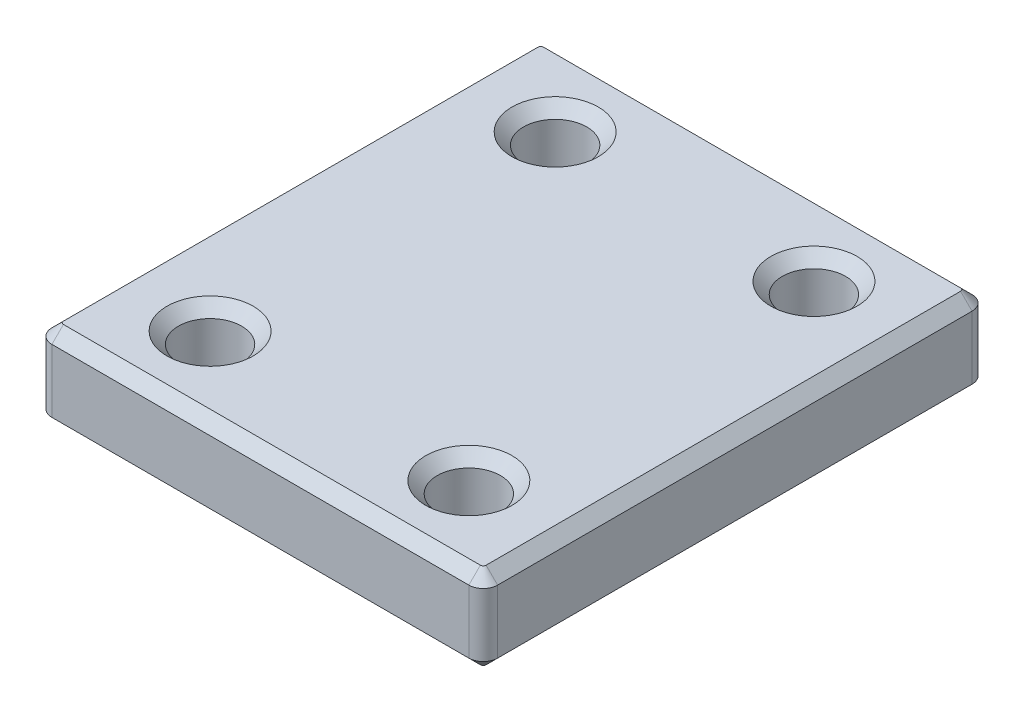
SolidWorks part; units mm, degrees
ref_plane "Front Plane" through (0, 0, 0) normal (0, 0, 1) x (1, 0, 0)
ref_plane "Top Plane" through (0, 0, 0) normal (0, 1, 0) x (1, 0, 0)
ref_plane "Right Plane" through (0, 0, 0) normal (1, 0, 0) x (0, 0, -1)
sketch "Sketch1" plane through (0, 0, 0) normal (0, 1, 0) x (1, 0, 0)
  line L1 (-15.5, -17.5) -> (15.5, -17.5)
  line L2 (-15.5, -17.5) -> (-15.5, 17.5)
  line L3 (-15.5, 17.5) -> (15.5, 17.5)
  line L4 (15.5, -17.5) -> (15.5, 17.5)
  line L5 (-15.5, -17.5) -> (15.5, 17.5) construction
  line L6 (-15.5, 17.5) -> (15.5, -17.5) construction
  point P0 (0, 0)
  dimension "D1" = 31
  dimension "D2" = 35
extrude "Boss-Extrude1" add sketch "Sketch1" along normal blind 6
sketch "Sketch2" plane through (0, 6, 0) normal (0, 1, 0) x (1, 0, 0)
  line L1 (-9, -12) -> (9, -12) construction
  line L2 (-9, -12) -> (-9, 12) construction
  line L3 (-9, 12) -> (9, 12) construction
  line L4 (9, -12) -> (9, 12) construction
  line L5 (-9, -12) -> (9, 12) construction
  line L6 (-9, 12) -> (9, -12) construction
  circle A0 centre (9, 12) radius 2.2
  circle A1 centre (9, -12) radius 2.2
  circle A2 centre (-9, 12) radius 2.2
  circle A3 centre (-9, -12) radius 2.2
  point P0 (0, 0)
  dimension "D1" = 4.4
  dimension "D2" = 18
  dimension "D3" = 24
extrude "Cut-Extrude1" cut sketch "Sketch2" against normal through all
fillet "Fillet1" radius 1 4 edges at (-15.5, 3, 17.5) (-15.5, 3, -17.5) (15.5, 3, -17.5) (15.5, 3, 17.5)
chamfer "Chamfer1" distance 0.8 angle 45 24 edges at (15.2071, 0, 17.2071) (15.5, 0, 0) (15.2071, 0, -17.2071) (0, 0, -17.5) (-15.2071, 0, -17.2071) (-15.5, 0, 0) (-15.2071, 0, 17.2071) (0, 0, 17.5) (9, 0, -9.8) (-9, 0, 14.2) (-9, 0, -9.8) (9, 0, 14.2) (-15.2071, 6, -17.2071) (0, 6, -17.5) (15.2071, 6, -17.2071) (15.5, 6, 0) (15.2071, 6, 17.2071) (0, 6, 17.5) (-15.2071, 6, 17.2071) (-15.5, 6, 0) (9, 6, -9.8) (-9, 6, 14.2) (-9, 6, -9.8) (9, 6, 14.2)
